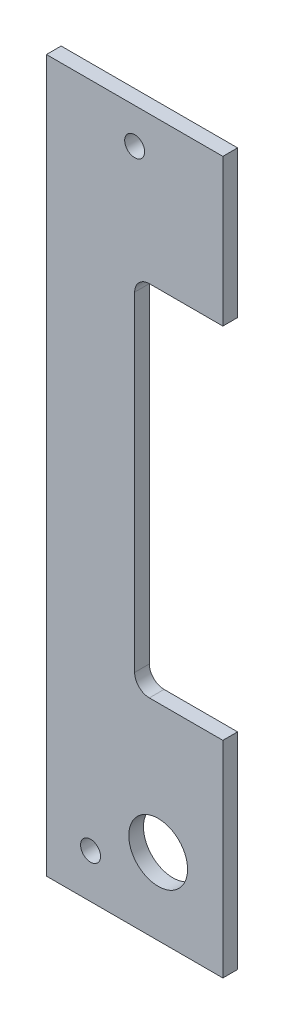
SolidWorks part; units mm, degrees
ref_plane "Front Plane" through (0, 0, 0) normal (0, 0, 1) x (1, 0, 0)
ref_plane "Top Plane" through (0, 0, 0) normal (0, 1, 0) x (1, 0, 0)
ref_plane "Right Plane" through (0, 0, 0) normal (1, 0, 0) x (0, 0, -1)
sketch "Sketch1" plane through (0, 0, 0) normal (0, 0, 1) x (1, 0, 0)
  line L8 (0, 0) -> (0, 44.45)
  line L9 (0, 44.45) -> (-15.875, 44.45)
  line L10 (-19.05, 47.625) -> (-19.05, 118.745)
  line L11 (-15.875, 121.92) -> (0, 121.92)
  line L12 (0, 121.92) -> (0, 153.67)
  line L13 (0, 153.67) -> (-38.1, 153.67)
  line L14 (-38.1, 153.67) -> (-38.1, 0)
  line L15 (-38.1, 0) -> (0, 0)
  line L16 (0, 0) -> (0, 44.45)
  line L17 (0, 44.45) -> (-15.875, 44.45)
  line L18 (-19.05, 47.625) -> (-19.05, 118.745)
  line L19 (-15.875, 121.92) -> (0, 121.92)
  line L20 (0, 121.92) -> (0, 153.67)
  line L21 (0, 153.67) -> (-38.1, 153.67)
  line L22 (-38.1, 153.67) -> (-38.1, 0)
  line L23 (-38.1, 0) -> (0, 0)
  arc A2 (-19.05, 47.625) -> (-15.875, 44.45) centre (-15.875, 47.625) ccw
  arc A3 (-15.875, 121.92) -> (-19.05, 118.745) centre (-15.875, 118.745) ccw
  arc A4 (-19.05, 47.625) -> (-15.875, 44.45) centre (-15.875, 47.625) ccw
  arc A5 (-15.875, 121.92) -> (-19.05, 118.745) centre (-15.875, 118.745) ccw
  dimension "D1" = 0
extrude "Boss-Extrude1" add sketch "Sketch1" along normal blind 3.175
hole_wizard "#6 Clearance Hole1" positions "Sketch3" profile "Sketch2" hole size "#6" standard "ANSI Inch" end condition through all
sketch "Sketch3" plane through (0, 0, 0) normal (0, 0, -1) x (-1, 0, 0)
  point P0 (28.575, 9.525)
  point P3 (19.05, 146.05)
sketch "Sketch2" plane through (-28.575, 9.525, 0) normal (1, 0, 0) x (0, 1, 0)
  line L0 (0, 0) -> (0, 3.175)
  line L1 (0, 3.175) -> (2.1526, 3.175)
  line L2 (2.1526, 3.175) -> (2.1526, 0)
  line L5 (2.1526, 0) -> (0, 0)
  line L11 (0, -6.35) -> (0, 107.95) construction
  dimension "Thru Hole Dia." = 4.3053
  dimension "Thru Hole Depth" = 3.175
hole_wizard "1/2 (0.5) Diameter Hole1" positions "Sketch5" profile "Sketch4" hole size "1/2" standard "ANSI Inch" end condition through all
sketch "Sketch5" plane through (0, 0, 0) normal (0, 0, -1) x (-1, 0, 0)
  point P0 (13.97, 16.51)
sketch "Sketch4" plane through (-13.97, 16.51, 0) normal (1, 0, 0) x (0, 1, 0)
  line L0 (0, 0) -> (0, 3.175)
  line L1 (0, 3.175) -> (6.35, 3.175)
  line L2 (6.35, 3.175) -> (6.35, 0)
  line L5 (6.35, 0) -> (0, 0)
  line L11 (0, -6.35) -> (0, 107.95) construction
  dimension "Thru Hole Dia." = 12.7
  dimension "Thru Hole Depth" = 3.175
